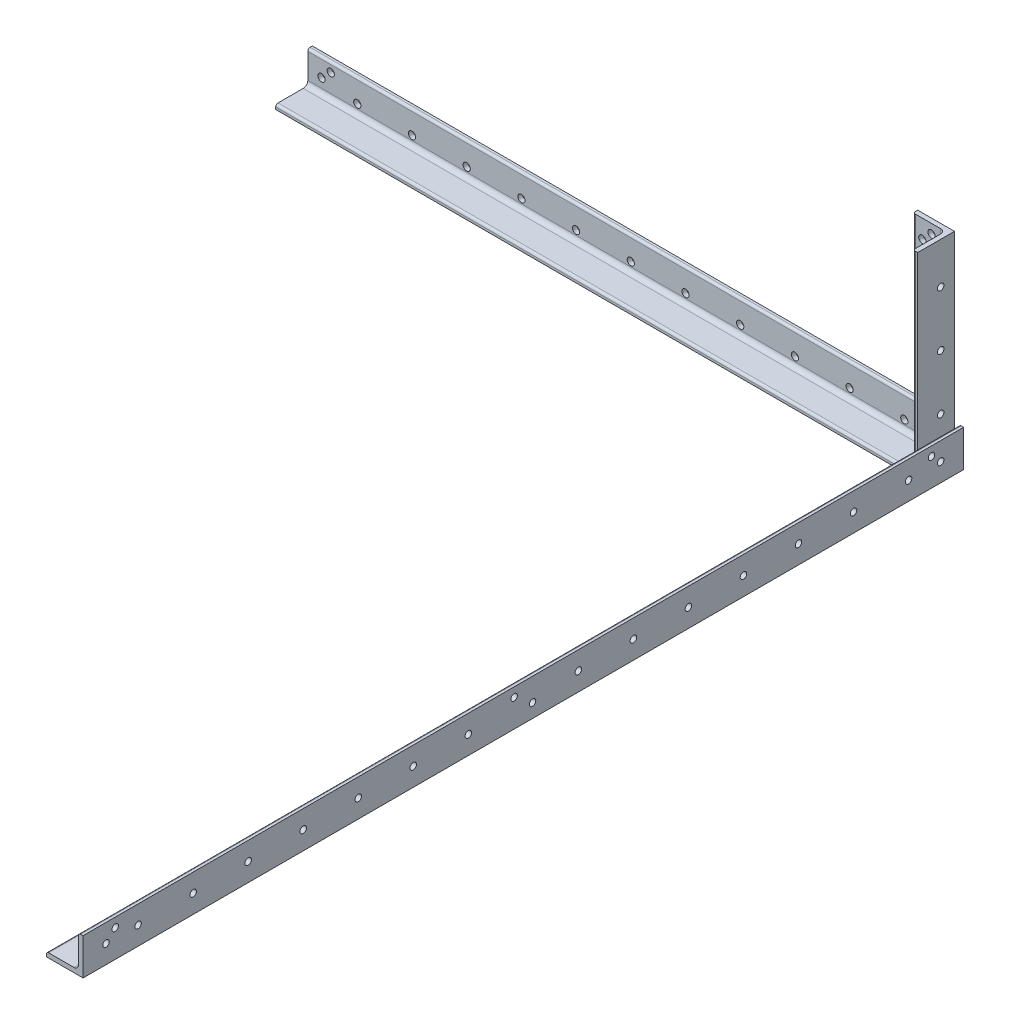
SolidWorks part; units mm, degrees
ref_plane "Front Plane" through (0, 0, 0) normal (0, 0, 1) x (1, 0, 0)
ref_plane "Top Plane" through (0, 0, 0) normal (0, 1, 0) x (1, 0, 0)
ref_plane "Right Plane" through (0, 0, 0) normal (1, 0, 0) x (0, 0, -1)
sketch "Sketch0" plane through (0, 0, 0) normal (0, 0, 1) x (1, 0, 0)
  line L0 (-12.7, -12.7) -> (12.7, -12.7)
  line L1 (12.7, -12.7) -> (12.7, 12.7)
  line L2 (12.7, 0) -> (0, 0) construction
  line L3 (0, 0) -> (0, -12.7) construction
  line L4 (9.525, -6.35) -> (9.525, 12.7) construction
  line L5 (6.35, -9.525) -> (-12.7, -9.525) construction
  arc A0 (9.525, -6.35) -> (6.35, -9.525) centre (6.35, -6.35) cw
  point P3 (8.5951, -8.5951)
  dimension "Inside Corner Radius" = 3.175
  dimension "Outside Height" = 25.4
  dimension "Inside Height" = 22.225
  dimension "Inside Width" = 22.225
  dimension "Wall Thickness" = 3.175
  dimension "D1" = 3.175
  dimension "Outside Width" = 25.4
sketch "Sketch1" plane through (0, 0, 0) normal (1, 0, 0) x (0, 0, -1)
  line L0 (304.8, 0) -> (-304.8, 0)
  point P4 (0, 0)
  dimension "Length" = 609.6
sketch "Sketch2" plane through (0, 0, 0) normal (0, 0, 1) x (1, 0, 0)
  line L0 (-12.7, -12.7) -> (12.7, -12.7)
  line L1 (12.7, -12.7) -> (12.7, 12.7)
  line L2 (12.7, 12.7) -> (9.525, 12.7) construction
  line L3 (9.525, 11.1125) -> (9.525, -6.35)
  line L4 (6.35, -9.525) -> (-11.1125, -9.525)
  line L5 (-12.7, -12.7) -> (-12.7, -9.525) construction
  line L6 (11.1125, 12.7) -> (12.7, 12.7)
  line L7 (-12.7, -11.1125) -> (-12.7, -12.7)
  line L8 (12.7, 0) -> (0, 0) construction
  line L9 (0, 0) -> (0, -12.7) construction
  arc A0 (9.525, 11.1125) -> (11.1125, 12.7) centre (11.1125, 11.1125) cw
  arc A1 (-12.7, -11.1125) -> (-11.1125, -9.525) centre (-11.1125, -11.1125) cw
  arc A2 (9.525, -6.35) -> (6.35, -9.525) centre (6.35, -6.35) cw
  dimension "Inside Radius" = 3.175
  dimension "Height" = 25.4
  dimension "Width" = 25.4
  dimension "Thickness" = 3.175
extrude "Boss-Extrude1" add sketch "Sketch2" along normal mid plane 609.6
sketch "Break Locations" plane through (0, 0, 0) normal (1, 0, 0) x (0, 0, -1)
  line L0 (-278.892, 0) -> (278.892, 0)
  line L1 (-304.8, -12.7) -> (-304.8, 12.7) construction
  line L2 (304.8, -12.7) -> (304.8, 12.7) construction
  point P0 (-283.21, 0)
  point P1 (283.21, 0)
  point P10 (0, 0)
  point P11 (278.892, 0)
  point P13 (-278.892, 0)
  dimension "D1" = 21.59
  dimension "D2" = 21.59
  dimension "D3" = 25.908
sketch "Sketch3" plane through (0, 0, -304.8) normal (0, 0, -1) x (-1, 0, 0)
  line L0 (-6.35, -9.525) -> (-6.35, 15.875)
  line L1 (-6.35, 15.875) -> (438.15, 15.875)
  line L2 (438.15, 15.875) -> (438.15, -9.525)
  line L3 (438.15, -9.525) -> (-6.35, -9.525)
  dimension "D1" = 25.4
  dimension "D2" = 444.5
extrude "Boss-Extrude2" add sketch "Sketch3" against normal blind 3.175 separate body
sketch "Sketch4" plane through (-438.15, 0, 0) normal (-1, 0, 0) x (0, 0, 1)
  line L1 (-304.8, -9.525) -> (-279.4, -9.525)
  line L2 (-304.8, -9.525) -> (-304.8, -6.35)
  line L3 (-304.8, -6.35) -> (-279.4, -6.35)
  line L4 (-279.4, -9.525) -> (-279.4, -6.35)
  dimension "D1" = 25.4
  dimension "D2" = 3.175
extrude "Boss-Extrude3" add sketch "Sketch4" against normal up to vertex (444.5 mm away)
fillet "Fillet1" radius 1.5875 2 edges at (-215.9, -6.35, -279.4) (-215.9, 15.875, -301.625)
fillet "Fillet2" radius 3.175 1 edges at (-215.9, -6.35, -301.625)
sketch "Sketch6" plane through (9.525, 0, 0) normal (-1, 0, 0) x (0, 0, 1)
  line L0 (-301.625, -3.175) -> (-301.625, 14.2875) construction
  line L1 (-301.625, -3.175) -> (-276.225, -3.175)
  line L2 (-301.625, -3.175) -> (-301.625, 0)
  line L3 (-301.625, 0) -> (-276.225, 0)
  line L4 (-276.225, -3.175) -> (-276.225, 0)
  line L5 (-301.625, -3.175) -> (-301.625, 14.2875) construction
  dimension "D1" = 25.4
  dimension "D2" = 3.175
extrude "Boss-Extrude4" add sketch "Sketch6" along normal blind 25.4 separate body
sketch "Sketch7" plane through (0, 0, 0) normal (0, 1, 0) x (1, 0, 0)
  line L1 (-15.875, 276.225) -> (6.35, 276.225)
  line L2 (-15.875, 276.225) -> (-15.875, 298.45)
  line L3 (-15.875, 298.45) -> (6.35, 298.45)
  line L4 (6.35, 276.225) -> (6.35, 298.45)
  dimension "D1" = 22.225
extrude "Cut-Extrude1" cut sketch "Sketch7" against normal blind 3.175
sketch "Sketch8" plane through (0, 0, 0) normal (0, 1, 0) x (1, 0, 0)
  line L6 (-15.875, 301.625) -> (-15.875, 298.45)
  line L7 (-15.875, 298.45) -> (6.35, 298.45)
  line L8 (6.35, 298.45) -> (6.35, 276.225)
  line L9 (6.35, 276.225) -> (9.525, 276.225)
  line L10 (9.525, 276.225) -> (9.525, 301.625)
  line L11 (9.525, 301.625) -> (-15.875, 301.625)
  line L12 (-15.875, 301.625) -> (-15.875, 298.45)
  line L13 (-15.875, 298.45) -> (6.35, 298.45)
  line L14 (6.35, 298.45) -> (6.35, 276.225)
  line L15 (6.35, 276.225) -> (9.525, 276.225)
  line L16 (9.525, 276.225) -> (9.525, 301.625)
  line L17 (9.525, 301.625) -> (-15.875, 301.625)
  dimension "D1" = 0
extrude "Boss-Extrude5" add sketch "Sketch8" along normal blind 130.175
fillet "Fillet3" radius 1.5875 2 edges at (6.35, 63.5, -276.225) (-15.875, 63.5, -298.45)
fillet "Fillet4" radius 3.175 1 edges at (6.35, 63.5, -298.45)
sketch "Sketch10" plane through (12.7, 0, 0) normal (1, 0, 0) x (0, 0, -1)
  line L1 (288.925, 0) -> (304.8, 0) construction
  line L2 (288.925, 0) -> (288.925, -12.7) construction
  line L3 (288.925, -12.7) -> (304.8, -12.7) construction
  line L4 (304.8, 0) -> (304.8, -12.7) construction
  line L5 (304.8, -12.7) -> (282.575, -12.7) construction
  line L6 (304.8, -12.7) -> (304.8, 6.35) construction
  line L7 (304.8, 6.35) -> (282.575, 6.35) construction
  line L8 (282.575, -12.7) -> (282.575, 6.35) construction
  circle A0 centre (282.575, 6.35) radius 2.25
  circle A1 centre (288.925, 0) radius 2.25
  dimension "D2" = 4.5
  dimension "D1" = 12.7
  dimension ".75" = 19.05
  dimension "D3" = 15.875
  dimension "D4" = 22.225
extrude "Cut-Extrude2" cut sketch "Sketch10" against normal blind 50.8
sketch "Sketch11" plane through (0, 0, -304.8) normal (0, 0, -1) x (-1, 0, 0)
  line L1 (-12.7, -12.7) -> (3.175, -12.7) construction
  line L2 (-12.7, -12.7) -> (-12.7, 3.175) construction
  line L3 (-12.7, 3.175) -> (3.175, 3.175) construction
  line L4 (3.175, -12.7) -> (3.175, 3.175) construction
  line L5 (-12.7, -12.7) -> (9.525, -12.7) construction
  line L6 (-12.7, -12.7) -> (-12.7, 9.525) construction
  line L7 (-12.7, 9.525) -> (9.525, 9.525) construction
  line L8 (9.525, -12.7) -> (9.525, 9.525) construction
  circle A0 centre (3.175, 3.175) radius 2.5
  circle A1 centre (9.525, 9.525) radius 2.5
  dimension "D3" = 5
  dimension "D1" = 15.875
  dimension "D2" = 22.225
  dimension "D4" = 15.875
  dimension "D5" = 22.225
extrude "Cut-Extrude3" cut sketch "Sketch11" against normal blind 50.8
sketch "Sketch12" plane through (12.7, 0, 0) normal (1, 0, 0) x (0, 0, -1)
  line L0 (0, 12.7) -> (0, -12.7) construction
  line L1 (-304.8, 12.7) -> (304.8, 12.7) construction
  line L2 (-304.8, -12.7) -> (304.8, -12.7) construction
  line L4 (-304.8, -12.7) -> (-304.8, 12.7) construction
  line L6 (-6.35, 6.35) -> (6.35, 6.35) construction
  line L7 (-6.35, 6.35) -> (-6.35, -3.175) construction
  line L8 (-6.35, -3.175) -> (6.35, -3.175) construction
  line L9 (6.35, 6.35) -> (6.35, -3.175) construction
  line L10 (-6.35, 6.35) -> (6.35, -3.175) construction
  line L11 (-6.35, -3.175) -> (6.35, 6.35) construction
  circle A0 centre (288.925, 0) radius 2.25 construction
  circle A1 centre (282.575, 6.35) radius 2.25 construction
  circle A2 centre (288.925, 0) radius 2.25
  circle A3 centre (282.575, 6.35) radius 2.25
  circle A4 centre (-288.925, 0) radius 2.25
  circle A5 centre (-282.575, 6.35) radius 2.25
  circle A19 centre (-6.35, 6.35) radius 2.25
  circle A20 centre (6.35, -3.175) radius 2.25
  circle A21 centre (-304.8, 0) radius 2.25 construction
  circle A22 centre (-266.7, 0) radius 2.25
  circle A23 centre (-228.6, 0) radius 2.25
  circle A24 centre (-190.5, 0) radius 2.25
  circle A25 centre (-152.4, 0) radius 2.25
  circle A26 centre (-114.3, 0) radius 2.25
  circle A27 centre (-76.2, 0) radius 2.25
  circle A28 centre (-38.1, 0) radius 2.25
  circle A76 centre (0, 0) radius 2.25 construction
  circle A77 centre (38.1, 0) radius 2.25
  circle A78 centre (76.2, 0) radius 2.25
  circle A79 centre (114.3, 0) radius 2.25
  circle A80 centre (152.4, 0) radius 2.25
  circle A81 centre (190.5, 0) radius 2.25
  circle A82 centre (228.6, 0) radius 2.25
  circle A83 centre (266.7, 0) radius 2.25
  circle A84 centre (304.8, 0) radius 2.25 construction
  point P44 (0, 1.5875)
  dimension "D2" = 22.225
  dimension "D3" = 9.525
  dimension "D4" = 6.35
  dimension "D5" = 12.7
  dimension "D1" = 17
extrude "Cut-Extrude4" cut sketch "Sketch12" against normal blind 50.8
sketch "Sketch13" plane through (0, 0, -304.8) normal (0, 0, -1) x (-1, 0, 0)
  line L0 (-12.7, -12.7) -> (-12.7, 12.7) construction
  line L1 (215.9, 15.875) -> (215.9, -9.525) construction
  line L2 (438.15, 15.875) -> (-6.35, 15.875) construction
  line L3 (-6.35, -9.525) -> (438.15, -9.525) construction
  circle A0 centre (-12.7, 0) radius 2.5 construction
  circle A1 centre (25.172, 0) radius 2.5
  circle A2 centre (63.0441, 0) radius 2.5
  circle A3 centre (100.9161, 0) radius 2.5
  circle A4 centre (138.7882, 0) radius 2.5
  circle A5 centre (176.6602, 0) radius 2.5
  circle A6 centre (214.5323, 0) radius 2.5
  circle A7 centre (252.4043, 0) radius 2.5
  circle A8 centre (290.2764, 0) radius 2.5
  circle A9 centre (328.1484, 0) radius 2.5
  circle A10 centre (366.0205, 0) radius 2.5
  circle A11 centre (403.8925, 0) radius 2.5
  circle A12 centre (441.7645, 0) radius 2.5 construction
  circle A13 centre (3.175, 3.175) radius 2.5 construction
  circle A14 centre (3.175, 3.175) radius 2.5
  circle A15 centre (9.525, 9.525) radius 2.5 construction
  circle A16 centre (9.525, 9.525) radius 2.5
  circle A17 centre (428.625, 3.175) radius 2.5
  circle A18 centre (422.275, 9.525) radius 2.5
  dimension "D2" = 22.225
  dimension "D1" = 13
extrude "Cut-Extrude5" cut sketch "Sketch13" against normal blind 50.8
sketch "Sketch14" plane through (0, 0, -304.8) normal (0, 0, -1) x (-1, 0, 0)
  line L0 (12.7, -12.7) -> (-12.7, -12.7) construction
  line L1 (-9.525, 63.5) -> (15.875, 63.5) construction
  line L2 (-9.525, 130.175) -> (-9.525, -3.175) construction
  line L3 (15.875, 130.175) -> (15.875, -3.175) construction
  circle A0 centre (0, -12.7) radius 2.5 construction
  circle A1 centre (0, 25.4) radius 2.5
  circle A2 centre (0, 63.5) radius 2.5
  circle A3 centre (0, 101.6) radius 2.5
  circle A4 centre (0, 139.7) radius 2.5
  circle A5 centre (3.175, 3.175) radius 2.5 construction
  circle A6 centre (9.525, 9.525) radius 2.5 construction
  circle A7 centre (3.175, 3.175) radius 2.5
  circle A8 centre (9.525, 9.525) radius 2.5
  circle A9 centre (3.175, 123.825) radius 2.5
  circle A10 centre (9.525, 117.475) radius 2.5
  dimension "D2" = 38.1
  dimension "D1" = 5
extrude "Cut-Extrude6" cut sketch "Sketch14" against normal blind 50.8
sketch "Sketch15" plane through (0, -12.7, 0) normal (0, -1, 0) x (1, 0, 0)
  circle A0 centre (4.102, -296.8961) radius 2.4715
  circle A1 centre (-8.1243, -284.9273) radius 2.8266
sketch "Sketch16" plane through (0, 0, -304.8) normal (0, 0, -1) x (-1, 0, 0)
  line L0 (-6.35, -9.525) -> (438.15, -9.525) construction
  line L1 (-6.35, 15.875) -> (-6.35, -9.525) construction
  circle A0 centre (3.175, 3.175) radius 2.5 construction
  circle A1 centre (9.525, 9.525) radius 2.5 construction
  circle A2 centre (25.172, 0) radius 2.5 construction
  circle A3 centre (3.175, 3.175) radius 2.5
  circle A4 centre (9.525, 9.525) radius 2.5
  circle A5 centre (25.172, 0) radius 2.5
  dimension "D1" = 12.7
  dimension "D2" = 9.525
  dimension "D3" = 19.05
  dimension "D4" = 9.525
sketch "Sketch17" plane through (0, 0, -301.625) normal (0, 0, -1) x (-1, 0, 0)
  line L0 (15.875, -3.175) -> (-9.525, -3.175) construction
  line L1 (-9.525, 130.175) -> (-9.525, -3.175) construction
  circle A0 centre (0, 25.4) radius 2.5 construction
  circle A1 centre (9.525, 9.525) radius 2.5 construction
  circle A2 centre (3.175, 3.175) radius 2.5 construction
  circle A3 centre (0, 25.4) radius 2.5
  circle A4 centre (9.525, 9.525) radius 2.5
  circle A5 centre (3.175, 3.175) radius 2.5
  dimension "D1" = 6.35
  dimension "D2" = 12.7
  dimension "D3" = 12.7
  dimension "D4" = 19.05
sketch "Sketch18" plane through (9.525, 0, 0) normal (1, 0, 0) x (0, 0, -1)
  line L0 (-304.8, -12.7) -> (304.8, -12.7) construction
  line L1 (304.8, 15.875) -> (304.8, -9.525) construction
  circle A0 centre (292.1, 25.4) radius 2.25
  circle A2 centre (282.575, 6.35) radius 2.25 construction
  circle A3 centre (292.1, 63.5) radius 2.25
  circle A4 centre (292.1, 101.6) radius 2.25
  dimension "D1" = 38.1
  dimension "D2" = 12.7
  dimension "D3" = 3
extrude "Cut-Extrude7" cut sketch "Sketch18" against normal blind 25.4
sketch "Sketch19" plane through (9.525, 0, 0) normal (1, 0, 0) x (0, 0, -1)
  line L0 (301.625, -3.175) -> (276.225, -3.175) construction
  line L1 (301.625, 130.175) -> (301.625, -3.175) construction
  circle A0 centre (288.925, 0) radius 2.25 construction
  circle A1 centre (282.575, 6.35) radius 2.25 construction
  circle A2 centre (288.925, 0) radius 2.25
  circle A3 centre (282.575, 6.35) radius 2.25
  dimension "D1" = 9.525
  dimension "D2" = 3.175
  dimension "D3" = 19.05
  dimension "D4" = 12.7
equation "\"D1@Break Locations\" = .85 * \"Height@Sketch2\""
equation "\"D2@Break Locations\"=\"D1@Break Locations\""
equation "\"Thickness@Sketch2\" = \"Wall Thickness@Sketch0\""
equation "\"Height@Sketch2\" = \"Outside Height@Sketch0\""
equation "\"Width@Sketch2\" = \"Outside Width@Sketch0\""
equation "\"Inside Radius@Sketch2\" = \"Inside Corner Radius@Sketch0\""
equation "\"Length@Boss-Extrude1\" = \"Length@Sketch1\""
equation "\"D3@Break Locations\"=\"D2@Break Locations\"*1.2"
equation "\"D1@Sketch0\"=\"Wall Thickness@Sketch0\""
